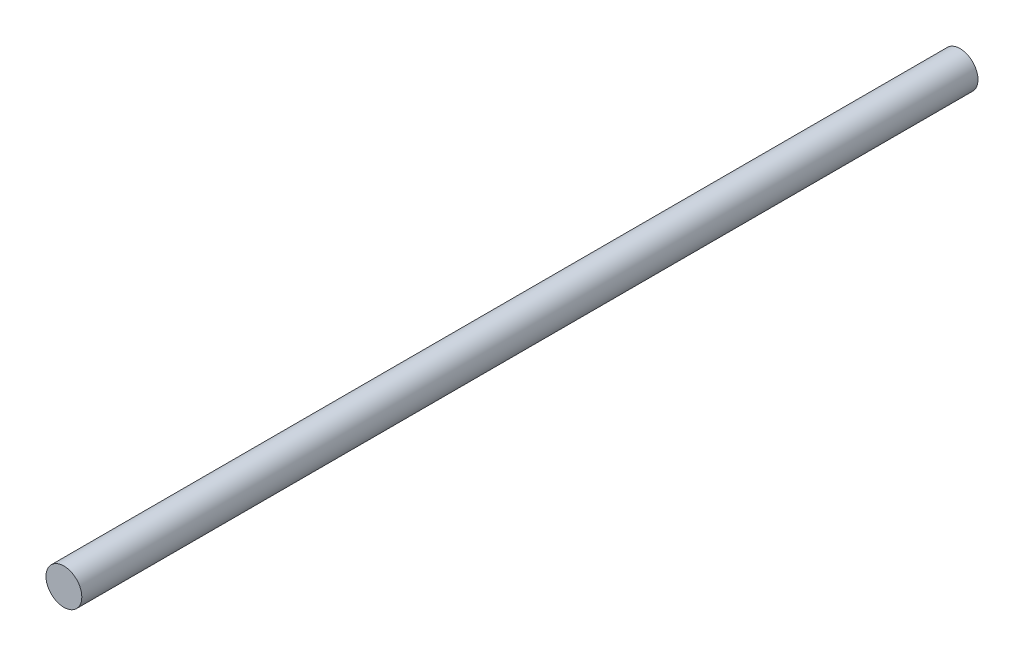
SolidWorks part; units mm, degrees
material "1.2083 (X42Cr13)"
ref_plane "Alzado" through (0, 0, 0) normal (0, 0, 1) x (1, 0, 0)
ref_plane "Planta" through (0, 0, 0) normal (0, 1, 0) x (1, 0, 0)
ref_plane "Vista lateral" through (0, 0, 0) normal (1, 0, 0) x (0, 0, -1)
sketch "Croquis1" plane through (0, 0, 0) normal (0, 0, 1) x (1, 0, 0)
  circle A0 centre (0, 0) radius 6
  dimension "D1" = 12
extrude "Saliente-Extruir1" add sketch "Croquis1" along normal blind 300
